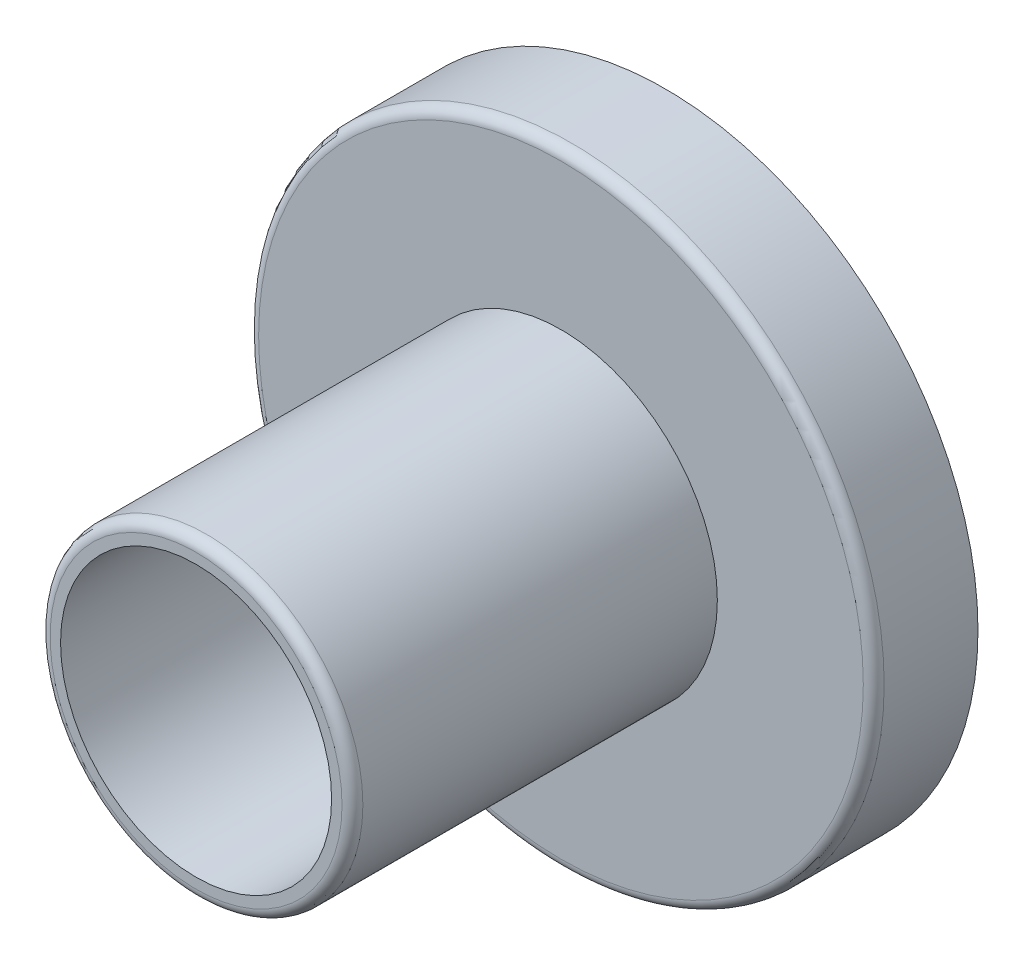
SolidWorks part; units mm, degrees
ref_plane "Alzado" through (0, 0, 0) normal (0, 0, 1) x (1, 0, 0)
ref_plane "Planta" through (0, 0, 0) normal (0, 1, 0) x (1, 0, 0)
ref_plane "Vista lateral" through (0, 0, 0) normal (1, 0, 0) x (0, 0, -1)
sketch "Croquis1" plane through (0, 0, 0) normal (0, 0, 1) x (1, 0, 0)
  circle A0 centre (0, 0) radius 30
extrude "Saliente-Extruir1" add sketch "Croquis1" along normal blind 10 contours A0
sketch "Croquis2" plane through (0, 0, 10) normal (0, 0, 1) x (1, 0, 0)
  circle A0 centre (0, 0) radius 15
extrude "Saliente-Extruir2" add sketch "Croquis2" along normal blind 35 contours A0
shell "Vaciado1" thickness 2
fillet "Redondeo1" radius 1 1 edges at (30, 0, 10)
fillet "Redondeo2" radius 1 1 edges at (15, 0, 45)
sketch "Croquis3" plane through (0, 0, 2) normal (0, 0, 1) x (1, 0, 0)
  circle A0 centre (0, 0) radius 5
extrude "Cortar-Extruir1" cut sketch "Croquis3" against normal up to next
